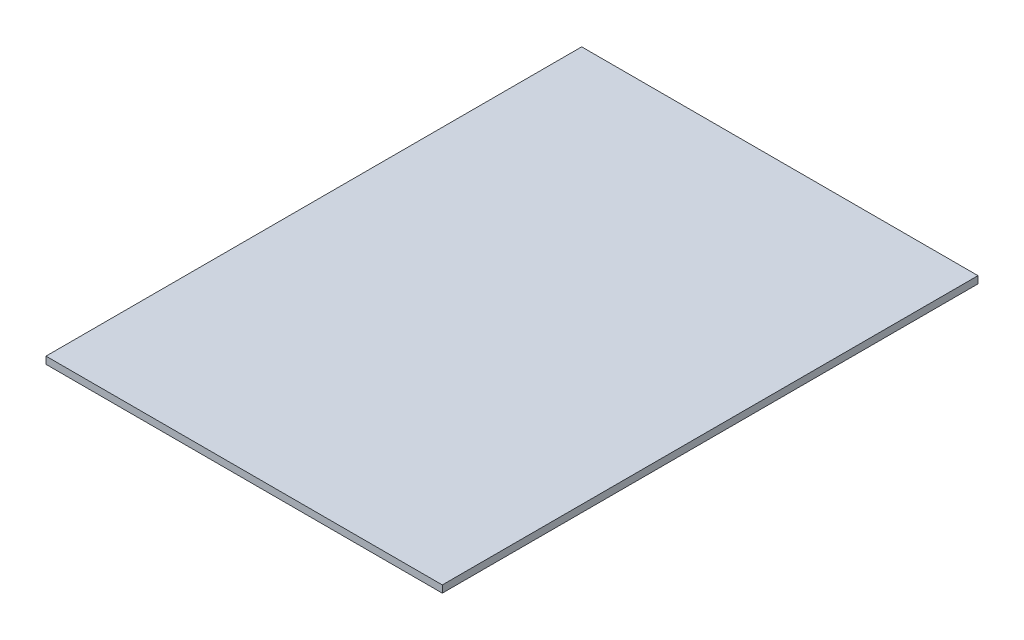
SolidWorks part; units mm, degrees
material "Polyurethane Foam Flexible"
ref_plane "Front Plane" through (0, 0, 0) normal (0, 0, 1) x (1, 0, 0)
ref_plane "Top Plane" through (0, 0, 0) normal (0, 1, 0) x (1, 0, 0)
ref_plane "Right Plane" through (0, 0, 0) normal (1, 0, 0) x (0, 0, -1)
sketch "Sketch1" plane through (0, 0, 0) normal (0, 1, 0) x (1, 0, 0)
  line L6 (-1055.878, 1427.226) -> (1055.878, 1427.226)
  line L15 (-1055.878, 1427.226) -> (-1055.878, -1427.226)
  line L16 (-1055.878, -1427.226) -> (1055.878, -1427.226)
  line L28 (1055.878, 1427.226) -> (1055.878, -1427.226)
  line L33 (-1055.878, 1427.226) -> (1055.878, -1427.226) construction
  line L34 (-1055.878, -1427.226) -> (1055.878, 1427.226) construction
  point P0 (0, 0)
  dimension "D1" = 2854.452
  dimension "D2" = 2111.756
extrude "Boss-Extrude1" add sketch "Sketch1" along normal blind 38.1
